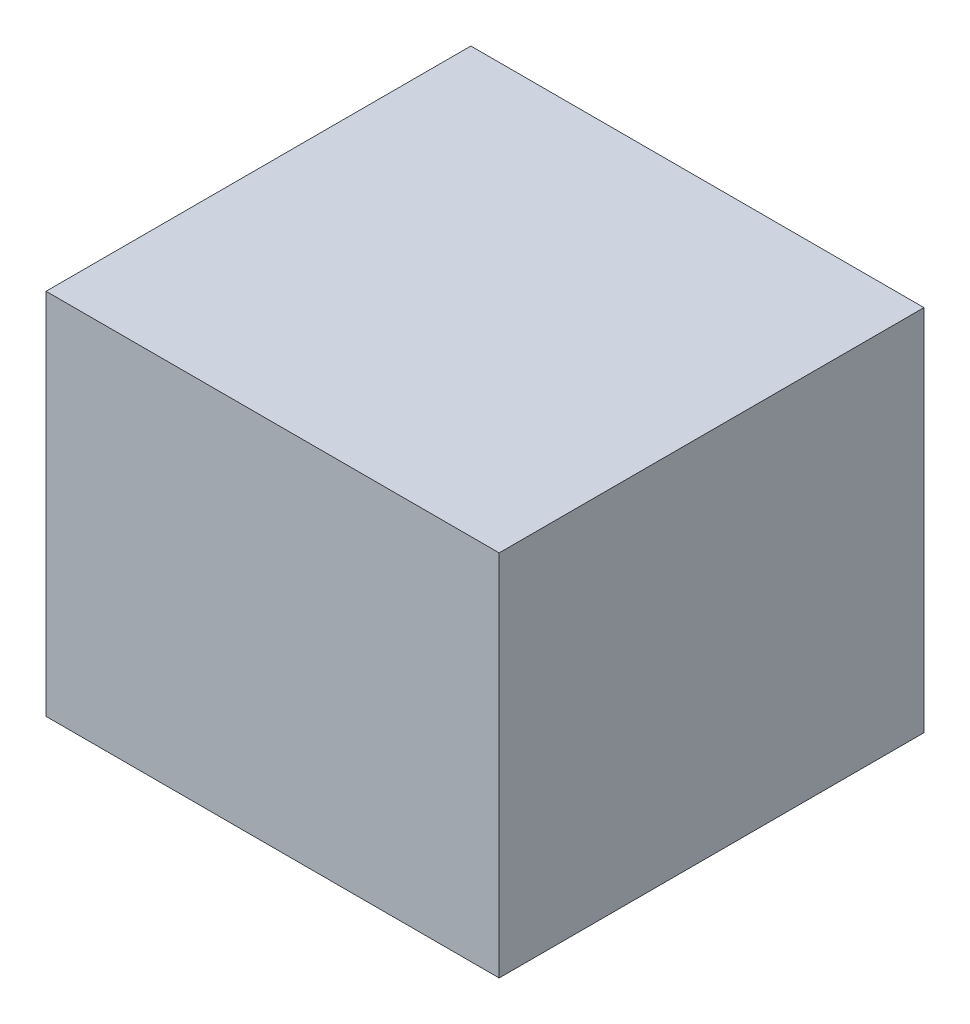
SolidWorks part; units mm, degrees
ref_plane "Front Plane" through (0, 0, 0) normal (0, 0, 1) x (1, 0, 0)
ref_plane "Top Plane" through (0, 0, 0) normal (0, 1, 0) x (1, 0, 0)
ref_plane "Right Plane" through (0, 0, 0) normal (1, 0, 0) x (0, 0, -1)
sketch "Sketch1" plane through (0, 0, 0) normal (0, 0, 1) x (1, 0, 0)
  line L1 (0, 0) -> (50.8, 0)
  line L2 (0, 0) -> (0, -41.275)
  line L3 (0, -41.275) -> (50.8, -41.275)
  line L4 (50.8, 0) -> (50.8, -41.275)
  dimension "D1" = 50.8
  dimension "D2" = 41.275
extrude "Boss-Extrude1" add sketch "Sketch1" along normal blind 47.625
